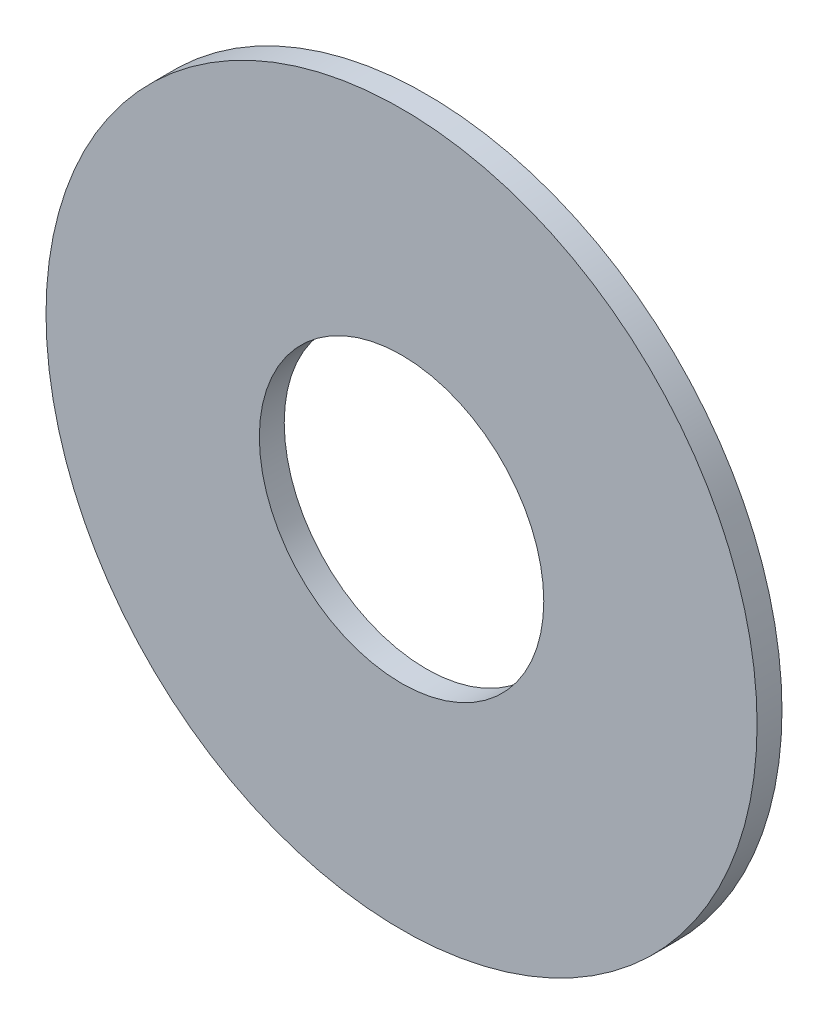
SolidWorks part; units mm, degrees
ref_plane "Plan de face" through (0, 0, 0) normal (0, 0, 1) x (1, 0, 0)
ref_plane "Plan de dessus" through (0, 0, 0) normal (0, 1, 0) x (1, 0, 0)
ref_plane "Plan de droite" through (0, 0, 0) normal (1, 0, 0) x (0, 0, -1)
sketch "Esquisse1" plane through (0, 0, 0) normal (0, 0, 1) x (1, 0, 0)
  circle A0 centre (0, 0) radius 10
  dimension "D1" = 20
extrude "Boss.-Extru.1" add sketch "Esquisse1" along normal blind 0.7
sketch "Esquisse2" plane through (0, 0, 0.7) normal (0, 0, 1) x (1, 0, 0)
  circle A0 centre (0, 0) radius 4
  dimension "D1" = 8
extrude "Enlèv. mat.-Extru.1" cut sketch "Esquisse2" against normal blind 1.5
